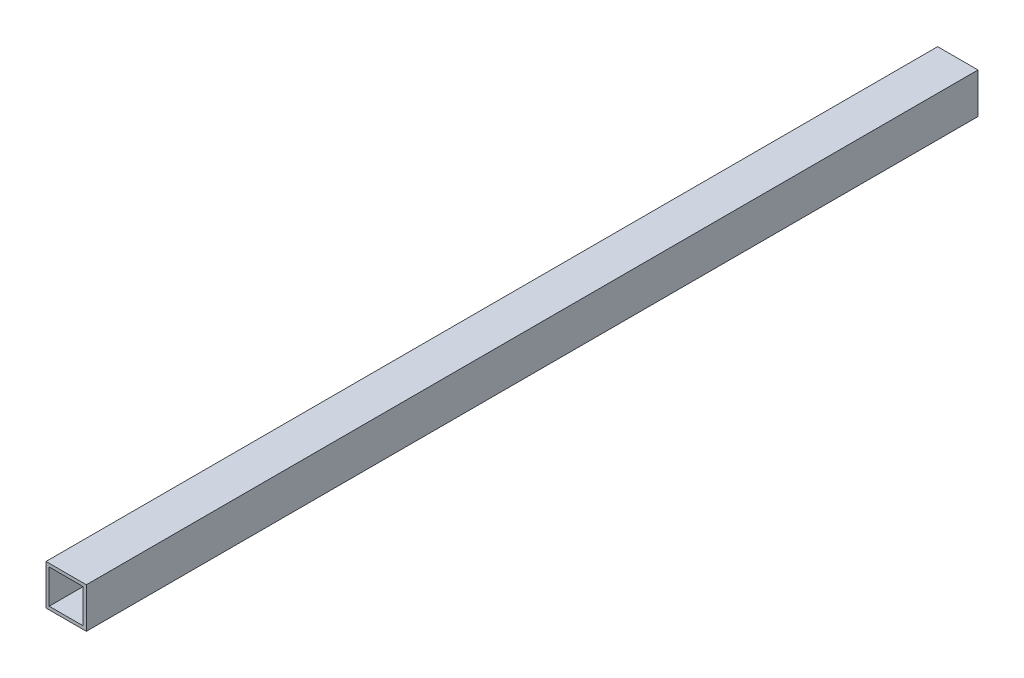
SolidWorks part; units mm, degrees
ref_plane "Front Plane" through (0, 0, 0) normal (0, 0, 1) x (1, 0, 0)
ref_plane "Top Plane" through (0, 0, 0) normal (0, 1, 0) x (1, 0, 0)
ref_plane "Right Plane" through (0, 0, 0) normal (1, 0, 0) x (0, 0, -1)
sketch "Sketch1" plane through (0, 0, 0) normal (0, 0, 1) x (1, 0, 0)
  line L0 (10.7, 10.7) -> (-10.7, 10.7)
  line L1 (12.7, 12.7) -> (-12.7, 12.7)
  line L2 (12.7, 12.7) -> (12.7, -12.7)
  line L3 (12.7, -12.7) -> (-12.7, -12.7)
  line L4 (-12.7, 12.7) -> (-12.7, -12.7)
  line L5 (12.7, 12.7) -> (-12.7, -12.7) construction
  line L6 (12.7, -12.7) -> (-12.7, 12.7) construction
  line L7 (-10.7, 10.7) -> (-10.7, -10.7)
  line L8 (10.7, -10.7) -> (-10.7, -10.7)
  line L9 (10.7, 10.7) -> (10.7, -10.7)
  point P0 (0, 0)
  dimension "D1" = 25.4
  dimension "D2" = 2
extrude "Boss-Extrude1" add sketch "Sketch1" along normal blind 561.2
